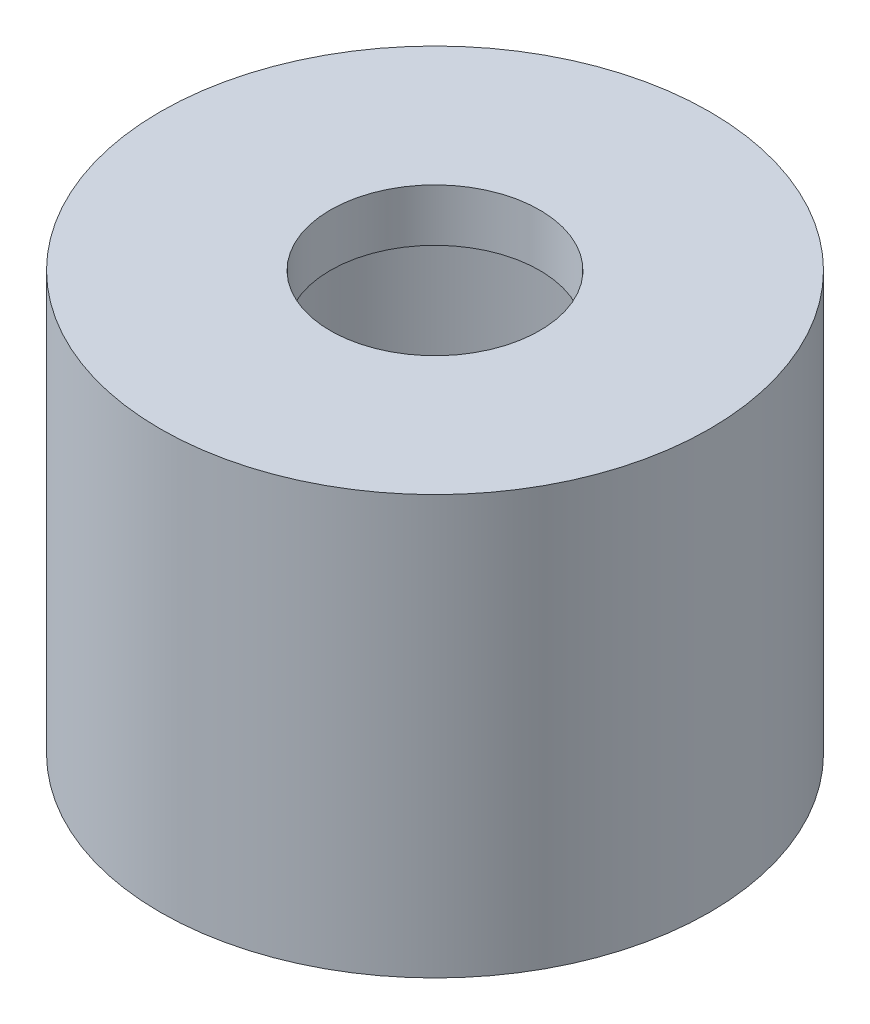
SolidWorks part; units mm, degrees
ref_plane "Plan de face" through (0, 0, 0) normal (0, 0, 1) x (1, 0, 0)
ref_plane "Plan de dessus" through (0, 0, 0) normal (0, 1, 0) x (1, 0, 0)
ref_plane "Plan de droite" through (0, 0, 0) normal (1, 0, 0) x (0, 0, -1)
sketch "Esquisse1" plane through (0, 0, 0) normal (0, 0, 1) x (1, 0, 0)
  line L0 (0, 0.7489) -> (0, -5.435) construction
  line L1 (-10.5, 0) -> (-4, 0)
  line L2 (-10.5, -16) -> (-8.5, -16)
  line L3 (-10.5, 0) -> (-10.5, -16)
  line L4 (-4, 0) -> (-4, -2)
  line L5 (-8.5, -2) -> (-4, -2)
  line L6 (0, 0) -> (0, -19) construction
  line L7 (-8.5, 0) -> (-4, 0) construction
  line L8 (-8.5, -2) -> (-8.5, -16)
  line L9 (-8.5, 0.7489) -> (-8.5, -5.435) construction
  line L11 (0, 0) -> (-10.5, 0) construction
  dimension "D3" = 2
  dimension "D1" = 16
  dimension "D2" = 6.5
  dimension "D4" = 4.5
  dimension "D5" = 4
revolve "Révolution1" add sketch "Esquisse1" angle 360 about L6
